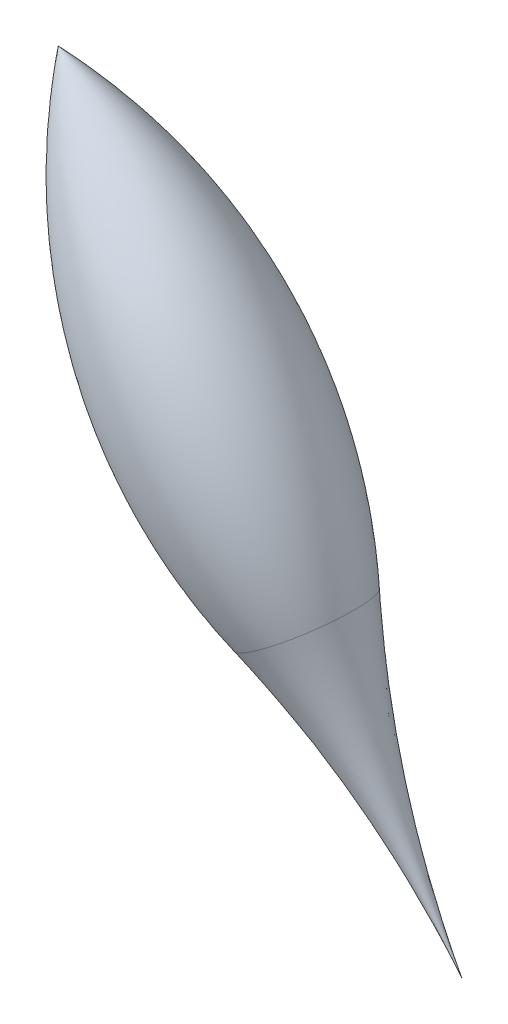
SolidWorks part; units mm, degrees
ref_plane "Front Plane" through (0, 0, 0) normal (0, 0, 1) x (1, 0, 0)
ref_plane "Top Plane" through (0, 0, 0) normal (0, 1, 0) x (1, 0, 0)
ref_plane "Right Plane" through (0, 0, 0) normal (1, 0, 0) x (0, 0, -1)
sketch "Sketch2" plane through (0, 0, 0) normal (0, 0, 1) x (1, 0, 0)
  line L0 (-50, 75) -> (50, -75)
  arc A0 (-50, 75) -> (0, -25) centre (75, 75) ccw
  arc A1 (0, -25) -> (50, -75) centre (-150, -225) cw
revolve "Revolve2" add sketch "Sketch2" angle 360 about L0
